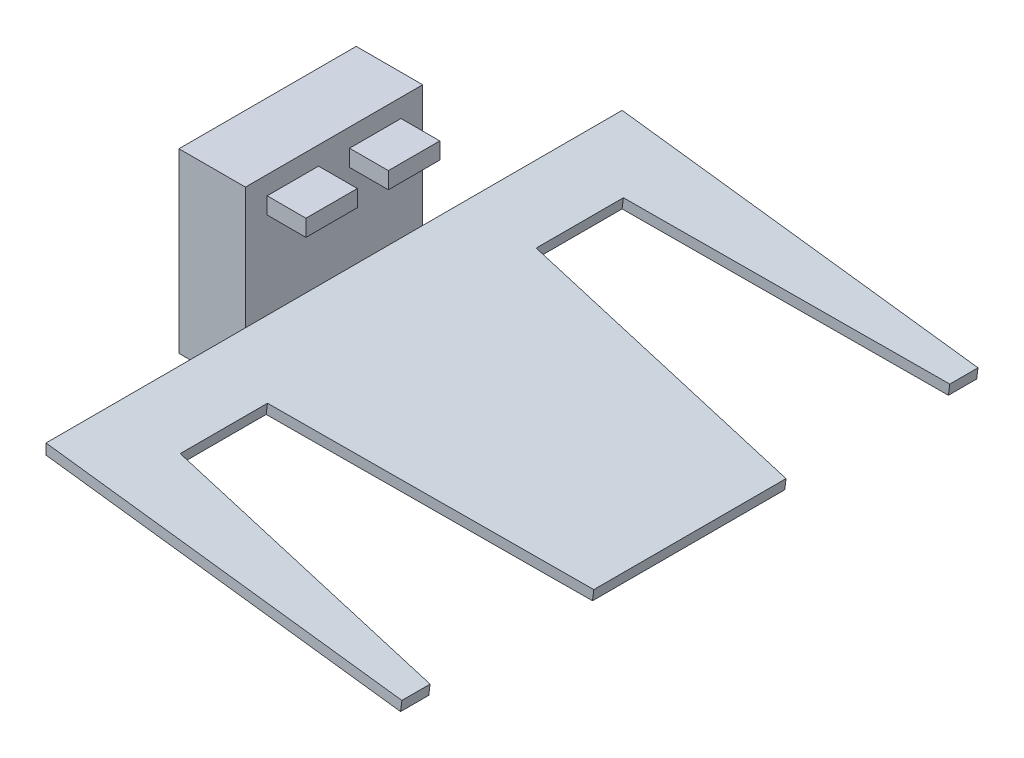
SolidWorks part; units mm, degrees
material "6061 Alloy"
ref_plane "Front Plane" through (0, 0, 0) normal (0, 0, 1) x (1, 0, 0)
ref_plane "Top Plane" through (0, 0, 0) normal (0, 1, 0) x (1, 0, 0)
ref_plane "Right Plane" through (0, 0, 0) normal (1, 0, 0) x (0, 0, -1)
sketch "Sketch1" plane through (0, 0, 0) normal (0, 0, 1) x (1, 0, 0)
  line L1 (-9.525, 50.8) -> (9.525, 50.8)
  line L2 (-9.525, 50.8) -> (-9.525, 0)
  line L3 (-9.525, 0) -> (9.525, 0)
  line L4 (9.525, 50.8) -> (9.525, 0)
  line L5 (-9.525, 50.8) -> (9.525, 0) construction
  line L6 (-9.525, 0) -> (9.525, 50.8) construction
  point P0 (0, 25.4)
  dimension "D1" = 50.8
  dimension "D2" = 19.05
extrude "Extrude1" add sketch "Sketch1" along normal mid plane 50.8
shell "Shell1" thickness 1.5875
sketch "Sketch3" plane through (0, 0, 0) normal (0, 0, 1) x (1, 0, 0)
  line L0 (9.525, 15.875) -> (111.5012, 2.9735)
  line L1 (9.525, 0) -> (9.525, 50.8) construction
  line L2 (135.0043, 0) -> (9.525, 0) construction
  line L3 (9.525, 0) -> (9.525, 15.875) construction
  line L4 (9.525, 12.8539) -> (111.125, 0)
  line L5 (9.1488, 12.9015) -> (134.6282, -2.9735) construction
  line L6 (111.125, 0) -> (111.5012, 2.9735)
  line L7 (9.525, 15.875) -> (135.0043, 0) construction
  line L8 (9.525, 15.875) -> (9.525, 12.8539)
  dimension "D1" = 101.6
  dimension "D2" = 15.875
  dimension "D3" = 2.9972
extrude "Extrude3" add sketch "Sketch3" along normal mid plane 165.1 separate body
ref_plane "Plane1" through (0, 0, 63.5) normal (0, 0, 1) x (1, 0, 0)
sketch "Sketch4" plane through (0, 0, 63.5) normal (0, 0, 1) x (1, 0, 0)
  line L0 (63.3371, 9.067) -> (28.938, 13.419)
  line L1 (-9.525, 0) -> (9.525, 0) construction
  line L3 (9.525, 0) -> (9.525, 50.8) construction
  line L4 (111.5012, 2.9735) -> (9.525, 15.875) construction
  arc A0 (28.938, 13.419) -> (63.3371, 9.067) centre (47.625, 23) ccw
  dimension "D2" = 42
  dimension "D1" = 23
  dimension "D3" = 38.1
extrude "Extrude4" cut sketch "Sketch4" against normal blind 25
mirror "Mirror1" about plane through (0, 0, 0) normal (0, 0, 1) of "Extrude4"
sketch "Sketch5" plane through (9.525, 0, 0) normal (1, 0, 0) x (0, 0, -1)
  line L0 (0, 50.8) -> (0, 0) construction
  line L1 (-19.177, 45.5278) -> (-4.445, 45.5278)
  line L2 (-19.177, 45.5278) -> (-19.177, 40.7653)
  line L3 (-19.177, 40.7653) -> (-4.445, 40.7653)
  line L4 (-4.445, 45.5278) -> (-4.445, 40.7653)
  line L6 (4.445, 45.5278) -> (4.445, 40.7653)
  line L7 (19.177, 40.7653) -> (4.445, 40.7653)
  line L8 (19.177, 45.5278) -> (19.177, 40.7653)
  line L9 (19.177, 45.5278) -> (4.445, 45.5278)
  line L11 (-25.4, 50.8) -> (25.4, 50.8) construction
  line L12 (-82.55, 2.9735) -> (82.55, 2.9735) construction
  dimension "D1" = 14.732
  dimension "D2" = 8.89
  dimension "D3" = 4.7625
  dimension "D4" = 37.7918
extrude "Extrude5" add sketch "Sketch5" along normal blind 11.1125 separate body
sketch "Sketch9" plane through (2.1268, 16.811, 0) normal (0.1255, 0.9921, 0) x (0.9921, -0.1255, 0)
  line L0 (27.0249, 38.5) -> (110.2462, 27.5437)
  line L1 (110.2462, -82.55) -> (110.2462, 82.55) construction
  line L2 (27.0249, 63.5) -> (110.2462, 74.4563)
  line L3 (0, 0) -> (110.2462, 0) construction
  line L4 (27.0249, -63.5) -> (110.2462, -74.4563)
  line L5 (27.0249, -38.5) -> (110.2462, -27.5437)
  line L6 (61.6982, 38.5) -> (27.0249, 38.5) construction
  line L7 (61.6982, 63.5) -> (27.0249, 63.5) construction
  line L8 (110.2462, 74.4563) -> (110.2462, 27.5437)
  line L9 (110.2462, -27.5437) -> (110.2462, -74.4563)
  line L10 (27.0249, 63.5) -> (27.0249, 38.5)
  line L11 (27.0249, -38.5) -> (27.0249, -63.5)
  dimension "D1" = 7.5
  dimension "D2" = 7.5
extrude "Extrude10" cut sketch "Sketch9" against normal up to next (2.9972 mm away)
